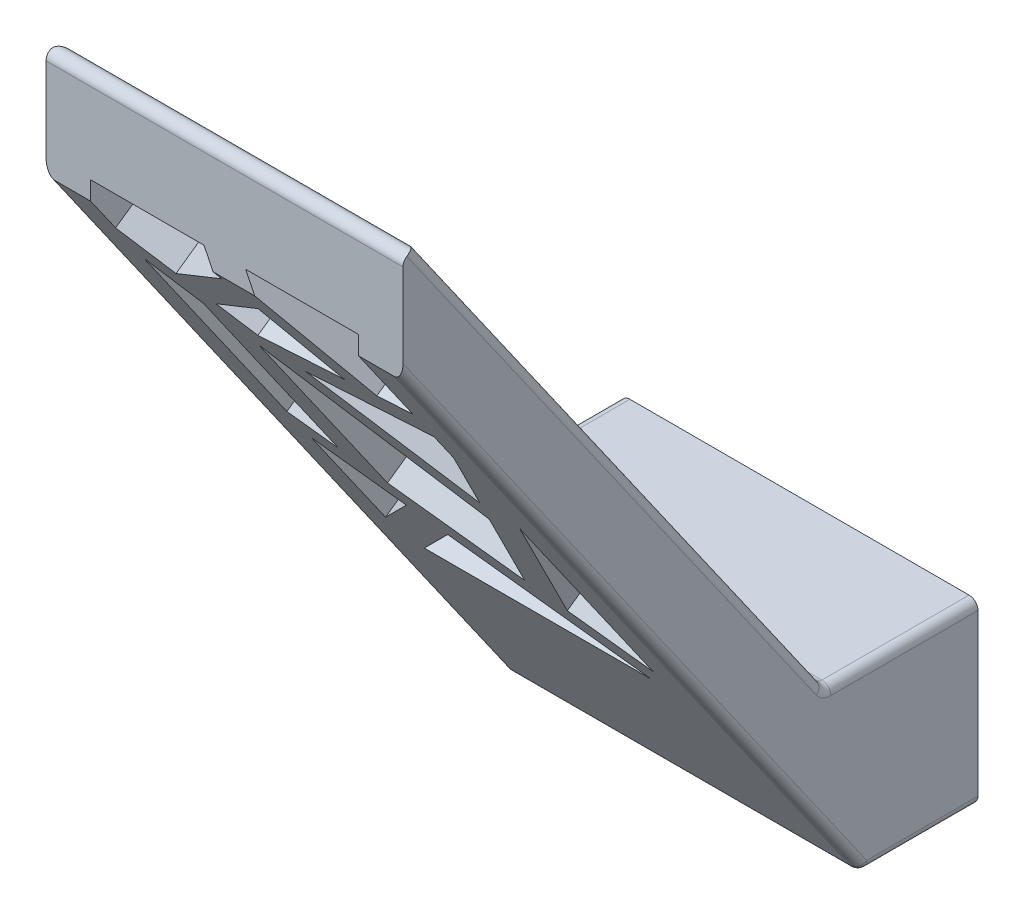
SolidWorks part; units mm, degrees
ref_plane "Front Plane" through (0, 0, 0) normal (0, 0, 1) x (1, 0, 0)
ref_plane "Top Plane" through (0, 0, 0) normal (0, 1, 0) x (1, 0, 0)
ref_plane "Right Plane" through (0, 0, 0) normal (1, 0, 0) x (0, 0, -1)
sketch "Sketch1" plane through (0, 0, 0) normal (0, 0, 1) x (1, 0, 0)
  line L1 (-73, 11.5) -> (-93, 11.5)
  line L2 (-73, 11.5) -> (-73, 21.5)
  line L3 (-73, 21.5) -> (-93, 21.5)
  line L4 (-93, 11.5) -> (-93, 21.5)
extrude "Boss-Extrude1" add sketch "Sketch1" along normal blind 5
sketch "Sketch2" plane through (-93, 0, 0) normal (-1, 0, 0) x (0, 0, 1)
  line L0 (0, 16.5) -> (5, 16.5) construction
  line L1 (0, 21.5) -> (0, 11.5) construction
  line L2 (5, 21.5) -> (5, 11.5) construction
  line L3 (5, 16.5) -> (1.499, 11.5)
  line L4 (5, 11.5) -> (0, 11.5) construction
  line L5 (1.499, 11.5) -> (6.499, 11.5)
  line L6 (6.499, 11.5) -> (32.2081, 48.2164)
  line L7 (8.501, 21.5) -> (32.2081, 55.3571)
  line L9 (32.2081, 55.3571) -> (32.2081, 48.2164)
  line L10 (5, 21.5) -> (8.501, 21.5)
  line L12 (5, 16.5) -> (5, 21.5)
  dimension "D1" = 35
  dimension "D2" = 5
extrude "Boss-Extrude2" add sketch "Sketch2" against normal up to surface (20 mm away) up to face at (-73, 16.5, 2.5)
sketch "Sketch3" plane through (0, 3.0791, -4.3974) normal (0, 0.5736, -0.8192) x (-1, 0, 0)
  line L0 (93, 58.8197) -> (73, 58.8197)
  line L1 (93, 63.8197) -> (93, 22.4878) construction
  line L2 (73, 22.4878) -> (73, 63.8197) construction
  line L3 (75.5, 58.8197) -> (75.5, 27.4878)
  line L4 (75.5, 27.4878) -> (90.5, 27.4878)
  line L5 (90.5, 27.4878) -> (90.5, 58.8197)
  line L6 (73, 63.8197) -> (93, 63.8197) construction
  line L7 (73, 22.4878) -> (93, 22.4878) construction
  line L8 (90.5, 38.8025) -> (88.3831, 37.4432)
  line L10 (76.5806, 27.4878) -> (84.9126, 32.8379)
  line L11 (90.5, 36.4257) -> (90.5, 38.8025)
  line L12 (80.76, 32.5482) -> (78.13, 40.6087)
  line L13 (75.5, 48.6691) -> (75.5, 42.2215)
  line L14 (75.5, 42.2215) -> (79.0207, 31.4314)
  line L16 (78.13, 40.6087) -> (86.3831, 48.6959)
  line L17 (90.5, 52.7301) -> (90.5, 55.5303)
  line L18 (90.5, 55.5303) -> (88.3347, 53.4085)
  line L20 (88.3831, 50.6557) -> (88.3831, 37.4432)
  line L22 (86.3831, 36.1589) -> (86.3831, 48.6959)
  line L24 (85.3975, 50.5303) -> (79.8807, 51.703)
  line L25 (75.5, 52.6342) -> (75.5, 50.5895)
  line L26 (75.5, 50.5895) -> (83.6828, 48.8501)
  line L28 (79.8807, 51.703) -> (82.3534, 55.8263)
  line L29 (84.1484, 58.8197) -> (81.8164, 58.8197)
  line L30 (81.8164, 58.8197) -> (77.8124, 52.1426)
  line L32 (83.3951, 57.5635) -> (88.3347, 53.4085)
  line L34 (86.8996, 52.0022) -> (82.3534, 55.8263)
  line L36 (75.5, 29.1707) -> (75.5, 27.4878)
  line L37 (76.5806, 27.4878) -> (75.5, 27.4878)
  line L38 (75.5, 27.4878) -> (75.5, 29.1707)
  line L39 (75.5, 27.4878) -> (76.5806, 27.4878)
  line L40 (75.5, 27.4878) -> (75.5, 29.1707)
  line L41 (90.5, 36.4257) -> (90.5, 38.8025)
  line L42 (84.9126, 32.8379) -> (89.293, 27.4878)
  line L43 (89.293, 27.4878) -> (90.5, 27.4878)
  line L44 (90.5, 29.1707) -> (86.6068, 33.9258)
  line L46 (90.5, 29.1707) -> (90.5, 27.4878)
  line L47 (76.5806, 27.4878) -> (75.5, 27.4878)
  line L48 (75.5, 29.1707) -> (75.5, 27.4878)
  line L49 (90.5, 36.4257) -> (90.5, 38.8025)
  line L50 (86.6068, 33.9258) -> (90.5, 36.4257)
  line L51 (79.0207, 31.4314) -> (75.5, 29.1707)
  line L52 (86.3831, 36.1589) -> (80.76, 32.5482)
  line L53 (77.4377, 42.7304) -> (75.5, 48.6691)
  line L54 (83.6828, 48.8501) -> (77.4377, 42.7304)
  line L55 (86.8996, 52.0022) -> (85.3975, 50.5303)
  line L56 (77.8124, 52.1426) -> (75.5, 52.6342)
  line L57 (83.3951, 57.5635) -> (84.1484, 58.8197)
  line L58 (88.3831, 50.6557) -> (90.5, 52.7301)
  point P42 (88.3831, 44.0495)
  dimension "D1" = 2.5
  dimension "D2" = 2.5
  dimension "D3" = 5
  dimension "D4" = 5
  dimension "D5" = 2
  dimension "D6" = 2
  dimension "D7" = 2
  dimension "D8" = 2
  dimension "D9" = 2
  dimension "D10" = 2
  dimension "D11" = 2
  dimension "D12" = 2
extrude "Cut-Extrude1" cut sketch "Sketch3" against normal up to surface (4.0958 mm away) contours L50 L44 L5 | L42 L10 L4 | L51 L14 L3 | L54 L26 L3 L53 | L56 L30 L0 L3 | L57 L32 L18 L5 L0 | L55 L34 L28 L24 | L58 L20 L8 L5 | L52 L22 L16 L12 up to face at (-83, 29.8582, 19.3535)
fillet "Fillet1" radius 0.5 45 edges at (-93, 21.5, 4.2505) (-73, 21.5, 4.2505) (-75.5, 43.733, 24.0688) (-76.4689, 40.5142, 21.8149) (-80.5603, 40.5883, 21.8668) (-79.5914, 43.8072, 24.1207) (-78.6582, 51.2614, 29.3402) (-75.5, 48.7279, 27.5662) (-76.6562, 45.9932, 25.6513) (-79.8144, 48.5266, 27.4253) (-82.9368, 25.5958, 11.3689) (-87.1028, 27.7871, 12.9033) (-80.7466, 27.7871, 12.9033) (-75.5, 32.3196, 16.077) (-77.2603, 27.9003, 12.9825) (-77.2603, 33.2455, 16.7254) (-90.5, 29.9458, 14.4148) (-88.5534, 31.8934, 15.7785) (-88.5534, 28.9219, 13.6979) (-83, 55.3571, 32.2081) (-73, 38.4286, 20.3545) (-93, 38.4286, 20.3545) (-83, 21.5, 8.501) (-81.1171, 47.1205, 26.4407) (-82.6391, 44.9514, 24.9219) (-86.1485, 45.0739, 25.0077) (-84.6265, 47.2431, 26.5265) (-89.4173, 47.6978, 26.8449) (-90.5, 49.9141, 28.3968) (-87.3242, 51.2614, 29.3402) (-83.7718, 50.7469, 28.9799) (-85.8649, 48.5306, 27.428) (-89.4415, 34.3075, 17.4689) (-90.5, 40.5687, 21.8531) (-89.4415, 45.4235, 25.2524) (-88.3831, 39.1623, 20.8683) (-82.2565, 39.6561, 21.2141) (-79.445, 33.0424, 16.5831) (-83.5715, 31.2199, 15.307) (-86.3831, 37.8336, 19.938) (-83, 11.5, 6.499) (-93, 29.8582, 19.3535) (-73, 29.8582, 19.3535) (-93, 11.5, 3.2495) (-73, 11.5, 3.2495)
sketch "Sketch4" plane through (0, 0, 0) normal (0, 0, -1) x (-1, 0, 0)
  circle A0 centre (78, 16.5) radius 0.5
  circle A1 centre (88, 16.5) radius 0.5
extrude "Cut-Extrude2" cut sketch "Sketch4" against normal offset from surface (8.7792 mm away) 1
